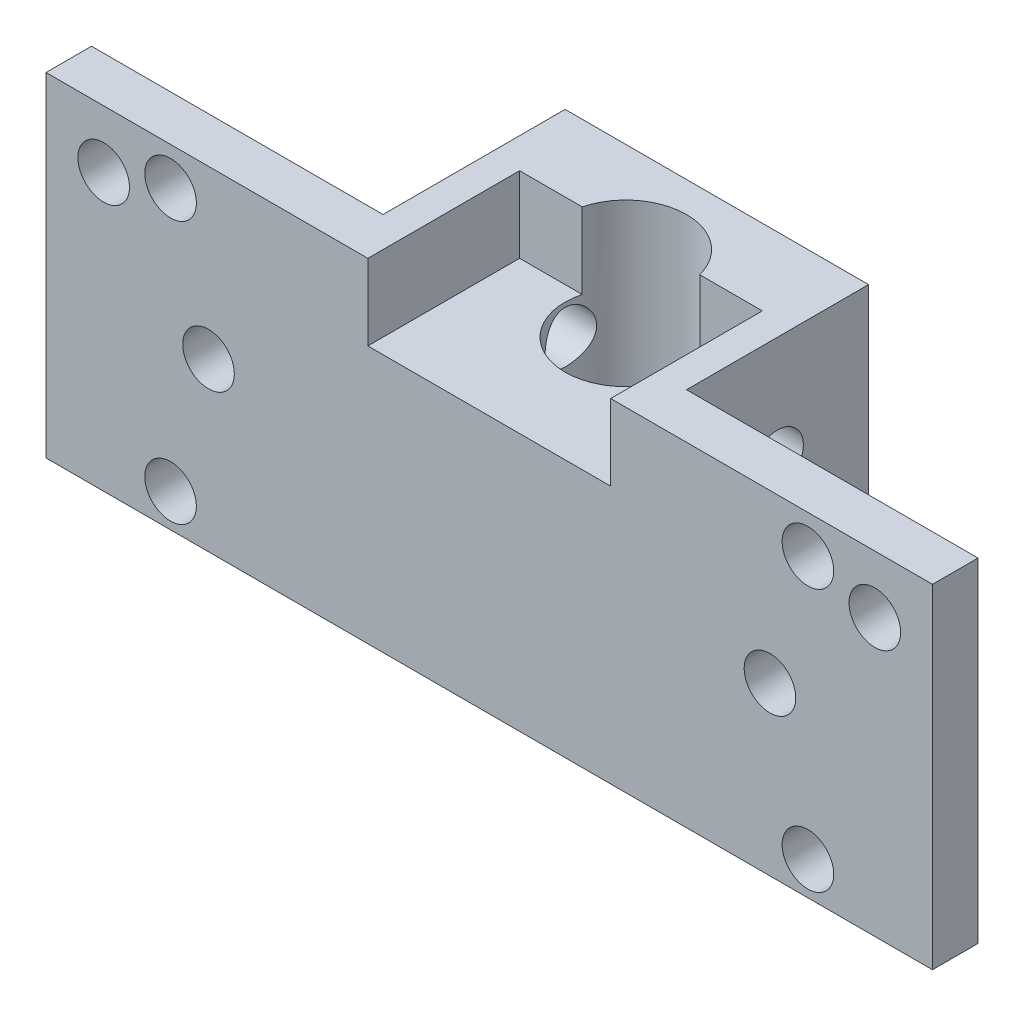
SolidWorks part; units mm, degrees
ref_plane "Plan de face" through (0, 0, 0) normal (0, 0, 1) x (1, 0, 0)
ref_plane "Plan de dessus" through (0, 0, 0) normal (0, 1, 0) x (1, 0, 0)
ref_plane "Plan de droite" through (0, 0, 0) normal (1, 0, 0) x (0, 0, -1)
sketch "Esquisse1" plane through (0, 0, 0) normal (0, 0, 1) x (1, 0, 0)
  line L1 (0, 0) -> (20, 0)
  line L2 (0, 0) -> (0, 22)
  line L3 (0, 22) -> (20, 22)
  line L4 (20, 0) -> (20, 22)
  dimension "D1" = 22
  dimension "D2" = 20
extrude "Boss.-Extru.1" add sketch "Esquisse1" along normal blind 12
sketch "Esquisse2" plane through (0, 22, 0) normal (0, 1, 0) x (1, 0, 0)
  line L0 (0, -6) -> (20, -6) construction
  line L1 (0, -12) -> (0, 0) construction
  line L2 (20, -12) -> (20, 0) construction
  circle A0 centre (10, -6) radius 4
extrude "Enlèv. mat.-Extru.1" cut sketch "Esquisse2" against normal blind 26
sketch "Esquisse3" plane through (20, 0, 0) normal (1, 0, 0) x (0, 0, -1)
  line L0 (-6, 22) -> (-6, 0) construction
  line L1 (-12, 22) -> (0, 22) construction
  line L2 (-12, 0) -> (0, 0) construction
  line L3 (-6, 11) -> (-3.1475, 11) construction
  circle A0 centre (-6, 15) radius 1.7
  circle A1 centre (-6, 7) radius 1.7
  dimension "D1" = 4
sketch "Esquisse4" plane through (0, 0, 12) normal (0, 0, 1) x (1, 0, 0)
  line L0 (10, 22) -> (10, 0) construction
  line L1 (20, 22) -> (0, 22) construction
  line L2 (0, 0) -> (20, 0) construction
  line L3 (39.21, 22) -> (39.21, 0)
  line L4 (39.21, 22) -> (-19.21, 22)
  line L5 (10, 22) -> (10, 0) construction
  line L6 (39.21, 0) -> (-19.21, 0)
  line L7 (-19.21, 22) -> (-19.21, 0)
  circle A0 centre (-15.41, 18.2) radius 1.7
  circle A1 centre (35.41, 18.2) radius 1.7
  dimension "D2" = 3.8
  dimension "D1" = 29.21
  dimension "D3" = 3.8
extrude "Boss.-Extru.2" add sketch "Esquisse4" along normal blind 3
sketch "Esquisse5" plane through (0, 0, 15) normal (0, 0, 1) x (1, 0, 0)
  line L0 (10, 22) -> (10, 0) construction
  line L1 (39.21, 22) -> (-19.21, 22) construction
  line L2 (-19.21, 0) -> (39.21, 0) construction
  line L3 (10, 11) -> (-14.9762, 11) construction
  circle A0 centre (-11, 19.5) radius 1.7
  circle A1 centre (-11, 2.2) radius 1.7
  circle A2 centre (31, 2.2) radius 1.7
  circle A3 centre (31, 19.5) radius 1.7
  circle A4 centre (-8.5, 11) radius 1.7
  circle A5 centre (28.5, 11) radius 1.7
  dimension "D3" = 2.5
  dimension "D4" = 18.5
  dimension "D1" = 21
  dimension "D2" = 17.3
extrude "Enlèv. mat.-Extru.2" cut sketch "Esquisse5" against normal blind 3
extrude "Enlèv. mat.-Extru.3" cut sketch "Esquisse3" against normal blind 27
sketch "Esquisse6" plane through (0, 0, 15) normal (0, 0, 1) x (1, 0, 0)
  line L0 (10, 22) -> (10, 0) construction
  line L1 (39.21, 22) -> (-19.21, 22) construction
  line L2 (-19.21, 0) -> (39.21, 0) construction
  line L3 (-19.21, 11) -> (39.21, 11) construction
  line L4 (-19.21, 22) -> (-19.21, 0) construction
  line L5 (39.21, 0) -> (39.21, 22) construction
  line L6 (18, 22) -> (18, 17)
  line L7 (2, 22) -> (18, 22)
  line L8 (2, 22) -> (2, 17)
  line L9 (2, 17) -> (18, 17)
  line L10 (10, 22) -> (10, 17) construction
  dimension "D1" = 5
  dimension "D2" = 8
extrude "Enlèv. mat.-Extru.4" cut sketch "Esquisse6" against normal blind 10
